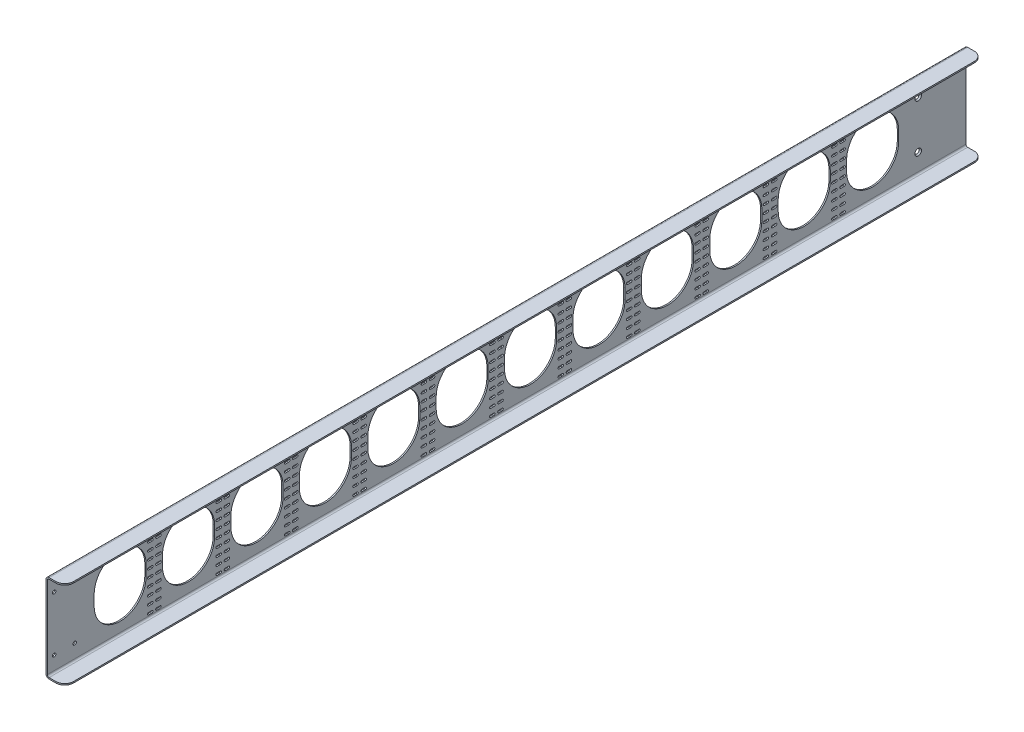
SolidWorks part; units mm, degrees
material "6061-T6 (SS)"
ref_plane "Front Plane" through (0, 0, 0) normal (0, 0, 1) x (1, 0, 0)
ref_plane "Top Plane" through (0, 0, 0) normal (0, 1, 0) x (1, 0, 0)
ref_plane "Right Plane" through (0, 0, 0) normal (1, 0, 0) x (0, 0, -1)
sketch "Sketch1" plane through (0, 0, 0) normal (0, 0, 1) x (1, 0, 0)
  line L0 (-12.7, 62.5) -> (12.7, -62.5) construction
  line L1 (-10.16, 62.5) -> (12.7, 62.5)
  line L2 (-12.7, 59.96) -> (-12.7, -59.96)
  line L3 (-10.16, -62.5) -> (12.7, -62.5)
  line L4 (12.7, 62.5) -> (12.7, -62.5) construction
  arc A0 (-12.7, -59.96) -> (-10.16, -62.5) centre (-10.16, -59.96) ccw
  arc A1 (-10.16, 62.5) -> (-12.7, 59.96) centre (-10.16, 59.96) ccw
  point P4 (0, 0)
  point P8 (-12.7, -62.5)
  dimension "D3" = 2.54
  dimension "D1" = 125
  dimension "D2" = 25.4
extrude "Extrude-Thin1" add sketch "Sketch1" along normal blind 1347.2339 thin thin type one direction reverse wall 2
hole_wizard "CSK for #10 Flat Head Machine Screw1" positions "Sketch3" profile "Sketch2" countersink size "#10" standard "ANSI Inch" end condition through all
sketch "Sketch3" plane through (-12.7, 0, 0) normal (1, 0, 0) x (0, 0, -1)
  line L0 (-70, 35) -> (-70, -35) construction
  line L2 (0, 0) -> (47.965, 0) construction
  line L3 (0, -59.96) -> (0, 59.96) construction
  point P0 (-70, -35)
  point P2 (-70, 35)
  point P12 (-70, 0)
  dimension "D1" = 70
  dimension "D2" = 70
sketch "Sketch2" plane through (-12.7, -35, 70) normal (0, 1, 0) x (0, 0, -1)
  line L0 (0, 0) -> (0, 2)
  line L1 (0, 2) -> (2.5527, 2)
  line L2 (2.5527, 2) -> (2.5527, 2.6882)
  line L3 (2.5527, 2.6882) -> (4.8895, 0)
  line L5 (4.8895, 0) -> (0, 0)
  line L6 (-2.5527, 2.6882) -> (-4.8895, 0) construction
  line L11 (0, -6.35) -> (0, 107.95) construction
  dimension "Thru Hole Dia." = 5.1054
  dimension "Thru Hole Depth" = 2
  dimension "Near C'Sink Dia." = 9.779
  dimension "Near C'Sink Angle" = 82
fillet "Fillet1" radius 13 4 edges at (12.7, -63.5, 1347.2339) (12.7, 63.5, 1347.2339) (12.7, -63.5, 0) (12.7, 63.5, 0)
hole_wizard "#10 Clearance Hole1" positions "Sketch5" profile "Sketch4" hole size "#10" standard "ANSI Inch" end condition through all
sketch "Sketch5" plane through (-14.7, 0, 0) normal (-1, 0, 0) x (0, 0, 1)
  line L1 (1307.2339, 40) -> (1337.2339, 40)
  line L2 (1307.2339, 40) -> (1307.2339, -40)
  line L3 (1307.2339, -40) -> (1337.2339, -40)
  line L4 (1337.2339, 40) -> (1337.2339, -40)
  line L5 (1307.2339, 40) -> (1337.2339, -40) construction
  line L6 (1307.2339, -40) -> (1337.2339, 40) construction
  line L7 (1347.2339, 0) -> (1380.8284, 0) construction
  line L8 (1347.2339, -59.96) -> (1347.2339, 59.96) construction
  point P0 (1337.2339, 40)
  point P99 (1307.2339, 40)
  point P101 (1307.2339, -40)
  point P103 (1337.2339, -40)
  point P112 (1322.2339, 0)
  dimension "D1" = 10
  dimension "D2" = 30
  dimension "D3" = 80
sketch "Sketch4" plane through (-14.7, 40, 1337.2339) normal (0, 1, 0) x (0, 0, 1)
  line L0 (0, 0) -> (0, 27.4)
  line L1 (0, 27.4) -> (2.4892, 27.4)
  line L2 (2.4892, 27.4) -> (2.4892, 0)
  line L5 (2.4892, 0) -> (0, 0)
  line L11 (0, -6.35) -> (0, 107.95) construction
  dimension "Thru Hole Dia." = 4.9784
  dimension "Thru Hole Depth" = 27.4
sketch "Sketch6" plane through (-14.7, 0, 0) normal (-1, 0, 0) x (0, 0, 1)
  line L0 (98.6169, 59.96) -> (98.6169, -112.8864) construction
  line L1 (1347.2339, 59.96) -> (0, 59.96) construction
  line L2 (1278.6169, 139.7438) -> (1278.6169, -112.8864) construction
  line L3 (70, 35) -> (1307.2339, 40) construction
  line L4 (688.6169, 37.5) -> (688.6169, 325.8875) construction
  line L5 (98.6169, -112.8864) -> (1278.6169, -112.8864) construction
  line L6 (0, 0) -> (-109.2733, 0) construction
  line L7 (0, -59.96) -> (0, 59.96) construction
  line L8 (136.7836, -7.5) -> (136.7836, 7.5) construction
  line L9 (98.6169, -7.5) -> (98.6169, 7.5)
  line L10 (174.9503, -7.5) -> (174.9503, 7.5)
  line L12 (174.9503, 55.4796) -> (174.9503, -64.1639) construction
  line L13 (198.9503, 55.4796) -> (198.9503, -80.1163) construction
  arc A0 (98.6169, -7.5) -> (174.9503, -7.5) centre (136.7836, -7.5) ccw
  arc A1 (174.9503, 7.5) -> (98.6169, 7.5) centre (136.7836, 7.5) ccw
  circle A4 centre (1307.2339, 40) radius 2.4892 construction
  circle A5 centre (70, 35) radius 3.1509 construction
  point P14 (688.6169, -112.8864)
  point P21 (136.7836, 0)
  dimension "D1" = 1180
  dimension "D2" = 76.3333
  dimension "D3" = 15
  dimension "D4" = 24
extrude "Cut-Extrude1" cut sketch "Sketch6" against normal through all
pattern_linear "LPattern1" count 12 spacing 100.3333 along (0, 0, 1) of "Cut-Extrude1"
sketch "Sketch7" plane through (-14.7, 0, 0) normal (-1, 0, 0) x (0, 0, 1)
  line L0 (0, 0) -> (-62.2329, 0) construction
  line L1 (0, -59.96) -> (0, 59.96) construction
  line L2 (167.6705, 58) -> (220.2831, 58) construction
  line L3 (138.8188, -58) -> (220.2831, -58) construction
  line L4 (220.2831, 58) -> (220.2831, -58) construction
  line L5 (174.9503, -55.6591) -> (198.9503, -55.6591) construction
  line L7 (174.9503, 7.5) -> (174.9503, -82.9973) construction
  line L8 (198.9503, 22.9088) -> (198.9503, -94.5541) construction
  line L9 (198.9503, 7.5) -> (198.9503, -7.5) construction
  line L10 (186.9503, -51.4004) -> (186.9503, -77.0118) construction
  line L11 (174.9503, -53.0212) -> (186.9503, -53.0212) construction
  line L12 (174.9503, -7.5) -> (174.9503, 7.5) construction
  line L13 (165.3655, -58) -> (165.3655, -55.6591) construction
  line L14 (165.3655, -56.8295) -> (167.6705, -56.8295) construction
  line L15 (178.4503, -56.8295) -> (183.4503, -56.8295) construction
  line L16 (178.4503, -55.242) -> (183.4503, -55.242)
  line L17 (178.4503, -58.417) -> (183.4503, -58.417)
  line L18 (195.4503, -56.8295) -> (190.4503, -56.8295) construction
  line L19 (195.4503, -55.242) -> (190.4503, -55.242)
  line L20 (195.4503, -58.417) -> (190.4503, -58.417)
  arc A1 (174.9503, 7.5) -> (98.6169, 7.5) centre (136.7836, 7.5) ccw construction
  arc A2 (178.4503, -55.242) -> (178.4503, -58.417) centre (178.4503, -56.8295) ccw
  arc A3 (183.4503, -58.417) -> (183.4503, -55.242) centre (183.4503, -56.8295) ccw
  arc A4 (195.4503, -55.242) -> (195.4503, -58.417) centre (195.4503, -56.8295) cw
  arc A5 (190.4503, -58.417) -> (190.4503, -55.242) centre (190.4503, -56.8295) cw
  point P8 (220.2831, 0)
  point P22 (186.9503, -55.6591)
  point P33 (180.9503, -56.8295)
  point P40 (192.9503, -56.8295)
  dimension "D1" = 116
  dimension "D2" = 2.3409
  dimension "D3" = 5
  dimension "D4" = 3.175
  dimension "D5" = 3.5
extrude "Cut-Extrude2" cut sketch "Sketch7" against normal through all
pattern_linear "LPattern2" count 11 spacing 11.4114 along (0, 1, 0) of "Cut-Extrude2"
pattern_linear "LPattern3" count 11 spacing 100.3333 along (0, 0, 1) of "LPattern2", "Cut-Extrude2"
